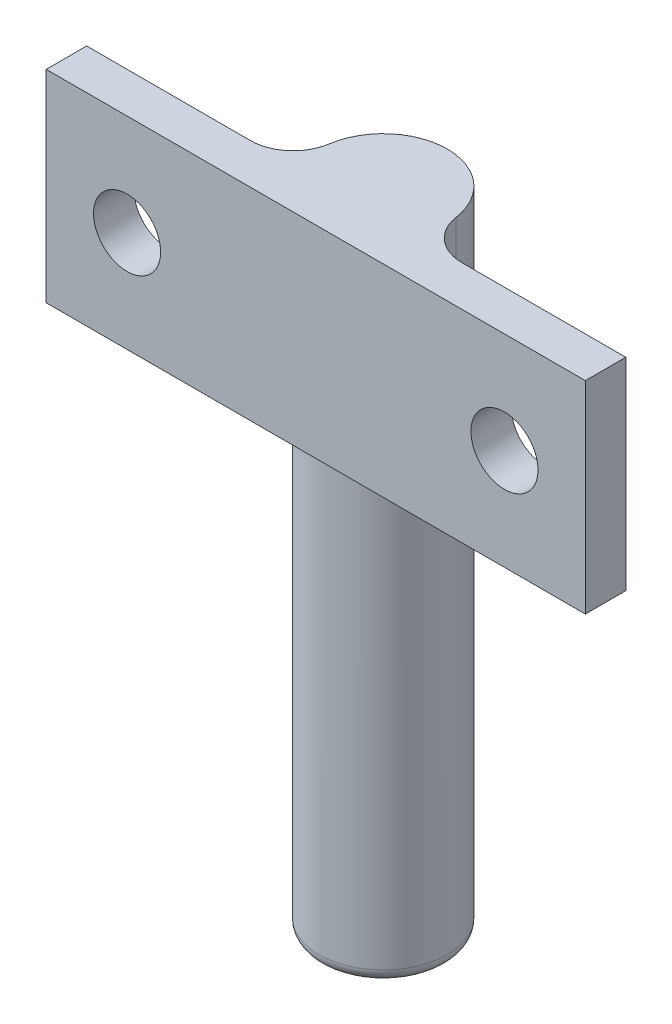
SolidWorks part; units mm, degrees
material "6061-T6 (SS)"
ref_plane "Front Plane" through (0, 0, 0) normal (0, 0, 1) x (1, 0, 0)
ref_plane "Top Plane" through (0, 0, 0) normal (0, 1, 0) x (1, 0, 0)
ref_plane "Right Plane" through (0, 0, 0) normal (1, 0, 0) x (0, 0, -1)
sketch "Sketch1" plane through (0, 0, 0) normal (0, 1, 0) x (1, 0, 0)
  line L0 (0, 0) -> (0, 15.3499) construction
  line L1 (-20, 3) -> (-4.3222, 3)
  line L2 (-20, 3) -> (-20, 0)
  line L3 (-20, 0) -> (20, 0)
  line L4 (20, 3) -> (20, 0)
  line L5 (4.3222, 3) -> (20, 3)
  arc A0 (4.3222, 3) -> (-4.3222, 3) centre (0, 5) ccw
  point P4 (0, 0)
  dimension "D3" = 9.525
  dimension "D1" = 40
  dimension "D2" = 3
  dimension "D4" = 5
extrude "Boss-Extrude1" add sketch "Sketch1" along normal blind 15
fillet "Fillet1" radius 3.175 2 edges at (-4.3222, 7.5, -3) (4.3222, 7.5, -3)
sketch "Sketch2" plane through (0, 0, 0) normal (0, -1, 0) x (1, 0, 0)
  circle A0 centre (0, -5) radius 4.7625
  arc A1 (-4.71, -5.705) -> (4.71, -5.705) centre (0, -5) ccw construction
extrude "Boss-Extrude2" add sketch "Sketch2" along normal blind 33
fillet "Fillet2" radius 1 1 edges at (0, -33, -9.7625)
hole_wizard "#10 Clearance Hole1" positions "Sketch4" profile "Sketch3" hole size "#10" standard "ANSI Inch" end condition through all
sketch "Sketch4" plane through (0, 0, -3) normal (0, 0, -1) x (-1, 0, 0)
  line L4 (0, 0) -> (0, 11.5234) construction
  line L5 (-14, 7.5) -> (0, 7.5) construction
  line L6 (14, 7.5) -> (0, 7.5) construction
  line L7 (-20, 15) -> (-20, 0) construction
  point P0 (14, 7.5)
  point P2 (-14, 7.5)
  point P30 (-20, 7.5)
  dimension "D1" = 28
sketch "Sketch3" plane through (-14, 7.5, -3) normal (1, 0, 0) x (0, 1, 0)
  line L0 (0, 0) -> (0, 3)
  line L1 (0, 3) -> (2.4892, 3)
  line L2 (2.4892, 3) -> (2.4892, 0)
  line L5 (2.4892, 0) -> (0, 0)
  line L11 (0, -6.35) -> (0, 107.95) construction
  dimension "Thru Hole Dia." = 4.9784
  dimension "Thru Hole Depth" = 3
